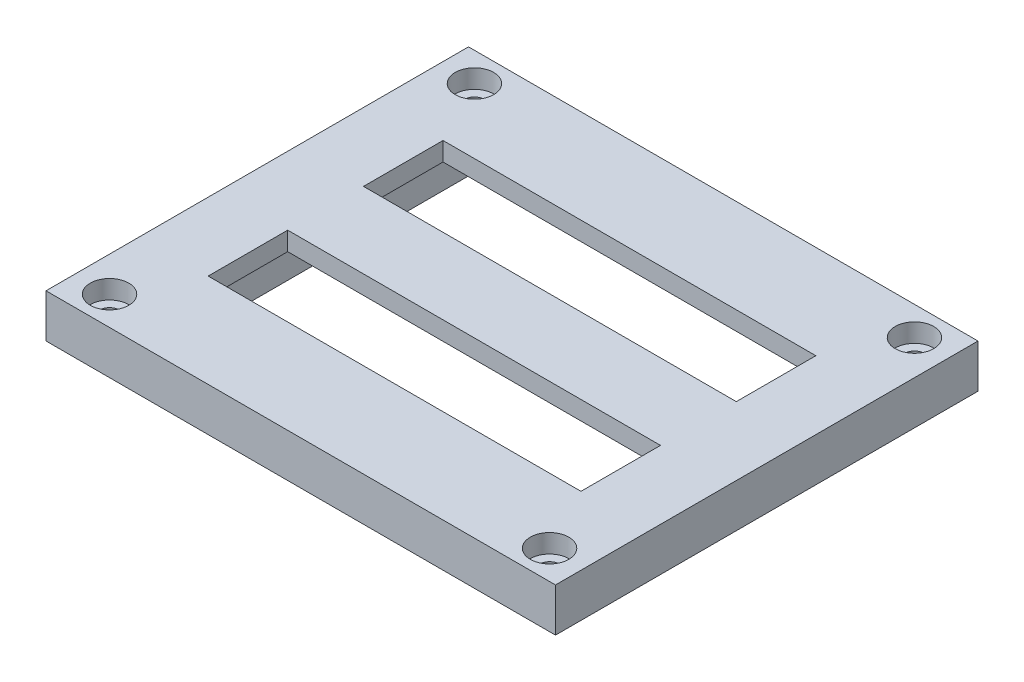
SolidWorks part; units mm, degrees
ref_plane "Спереди" through (0, 0, 0) normal (0, 0, 1) x (1, 0, 0)
ref_plane "Сверху" through (0, 0, 0) normal (0, 1, 0) x (1, 0, 0)
ref_plane "Справа" through (0, 0, 0) normal (1, 0, 0) x (0, 0, -1)
sketch "Sketch1" plane through (0, 0, 0) normal (0, 1, 0) x (1, 0, 0)
  line L1 (38, -31) -> (-38, -31)
  line L2 (38, -31) -> (38, 31)
  line L3 (38, 31) -> (-38, 31)
  line L4 (-38, -31) -> (-38, 31)
  line L5 (38, -31) -> (-38, 31) construction
  line L6 (38, 31) -> (-38, -31) construction
  point P0 (0, 0)
  dimension "D1" = 76
  dimension "D2" = 62
extrude "Boss-Extrude1" add sketch "Sketch1" along normal blind 2
sketch "Sketch2" plane through (0, 2, 0) normal (0, 1, 0) x (1, 0, 0)
  line L1 (-41, 34) -> (41, 34)
  line L2 (-41, 34) -> (-41, -34)
  line L3 (-41, -34) -> (41, -34)
  line L4 (41, 34) -> (41, -34)
  line L5 (-41, 34) -> (41, -34) construction
  line L6 (-41, -34) -> (41, 34) construction
  point P0 (0, 0)
  dimension "D1" = 82
  dimension "D2" = 68
extrude "Boss-Extrude2" add sketch "Sketch2" along normal blind 8
sketch "Sketch3" plane through (0, 0, 0) normal (0, -1, 0) x (1, 0, 0)
  line L0 (38, 0) -> (-38, 0) construction
  line L1 (0, -31) -> (0, 31) construction
  line L2 (38, -31) -> (-38, -31) construction
  line L3 (38, 31) -> (38, -31) construction
  line L4 (-38, -31) -> (-38, 31) construction
  line L5 (-38, 31) -> (38, 31) construction
  line L7 (-30, -18.9) -> (30, -18.9)
  line L8 (-30, -18.9) -> (-30, -6.1)
  line L9 (-30, 18.9) -> (30, 18.9)
  line L10 (-30, 18.9) -> (-30, 6.1)
  line L11 (-30, 6.1) -> (30, 6.1)
  line L12 (30, 18.9) -> (30, 6.1)
  line L13 (-30, 18.9) -> (30, 6.1) construction
  line L14 (-30, 6.1) -> (30, 18.9) construction
  line L15 (-30, -6.1) -> (30, -6.1)
  line L16 (30, -18.9) -> (30, -6.1)
  line L17 (-30, -18.9) -> (30, -6.1) construction
  line L18 (-30, -6.1) -> (30, -18.9) construction
  point P6 (0, 12.5)
  point P9 (0, -12.5)
  dimension "D1" = 60
  dimension "D2" = 12.8
  dimension "D3" = 25
  dimension "D4" = 12.5
extrude "Cut-Extrude1" cut sketch "Sketch3" against normal through all
sketch "Sketch4" plane through (0, 10, 0) normal (0, 1, 0) x (1, 0, 0)
  line L0 (41, 34) -> (-41, -34) construction
  line L1 (-41, 34) -> (41, -34) construction
  line L2 (-35.4089, 29.3635) -> (35.4089, 29.3635) construction
  line L3 (35.4089, 29.3635) -> (35.4089, -29.3635) construction
  line L4 (35.4089, -29.3635) -> (-35.4089, -29.3635) construction
  line L5 (-35.4089, -29.3635) -> (-35.4089, 29.3635) construction
  line L7 (-35.4089, -29.3635) -> (35.4089, 29.3635) construction
  line L8 (-35.4089, 29.3635) -> (35.4089, -29.3635) construction
  circle A0 centre (-35.4089, 29.3635) radius 1.6
  circle A1 centre (35.4089, 29.3635) radius 1.6
  circle A2 centre (35.4089, -29.3635) radius 1.6
  circle A3 centre (-35.4089, -29.3635) radius 1.6
  point P8 (0, 0)
  dimension "D2" = 3.2
  dimension "D1" = 92
extrude "Cut-Extrude2" cut sketch "Sketch4" against normal through all
sketch "Sketch5" plane through (0, 10, 0) normal (0, 1, 0) x (1, 0, 0)
  circle A0 centre (-35.4089, 29.3635) radius 3.1
  circle A1 centre (35.4089, 29.3635) radius 3.1
  circle A2 centre (35.4089, -29.3635) radius 3.1
  circle A3 centre (-35.4089, -29.3635) radius 3.1
  dimension "D1" = 6.2
extrude "Cut-Extrude3" cut sketch "Sketch5" against normal blind 3
sketch "Sketch9" plane through (0, 0, 0) normal (0, -1, 0) x (1, 0, 0)
  line L0 (-38, 31) -> (38, 31) construction
  line L1 (37.8, -30.8) -> (-37.8, -30.8)
  line L2 (37.8, -30.8) -> (37.8, 30.8)
  line L3 (37.8, 30.8) -> (-37.8, 30.8)
  line L4 (-37.8, -30.8) -> (-37.8, 30.8)
  line L5 (37.8, -30.8) -> (-37.8, 30.8) construction
  line L6 (37.8, 30.8) -> (-37.8, -30.8) construction
  line L7 (-38, -31) -> (-38, 31) construction
  point P0 (0, 0)
  dimension "D1" = 0.2
  dimension "D2" = 0.2
extrude "Cut-Extrude5" cut sketch "Sketch9" against normal blind 3 flip side to cut
sketch "Sketch10" plane through (0, 0, 0) normal (0, -1, 0) x (1, 0, 0)
  line L0 (-37.8, -30.8) -> (-31.8, -30.8)
  line L1 (-37.8, 24.8) -> (-37.8, 30.8)
  line L2 (34.7044, -30.8) -> (-34.7044, -30.8) construction
  line L3 (-37.8, 30.8) -> (-31.8, 30.8)
  line L4 (-31.8, -30.8) -> (-37.8, -24.8)
  line L5 (-37.8, 30.8) -> (-37.8, -30.8) construction
  line L6 (-37.8, -24.8) -> (-37.8, -30.8)
  line L7 (-34.7044, 30.8) -> (34.7044, 30.8) construction
  line L8 (-31.8, 30.8) -> (-37.8, 24.8)
  line L9 (37.8, 30.8) -> (37.8, 24.8)
  line L10 (37.8, -30.8) -> (37.8, 30.8) construction
  line L11 (37.8, 24.8) -> (31.8, 30.8)
  line L12 (31.8, 30.8) -> (37.8, 30.8)
  line L13 (37.8, -30.8) -> (31.8, -30.8)
  line L14 (31.8, -30.8) -> (37.8, -24.8)
  line L15 (37.8, -24.8) -> (37.8, -30.8)
  dimension "D1" = 6
extrude "Cut-Extrude6" cut sketch "Sketch10" against normal blind 3
sketch "Sketch11" plane through (0, 0, 0) normal (0, -1, 0) x (1, 0, 0)
  line L1 (-33, -27) -> (33, -27)
  line L2 (-33, -27) -> (-33, 27)
  line L3 (-33, 27) -> (33, 27)
  line L4 (33, -27) -> (33, 27)
  line L5 (-33, -27) -> (33, 27) construction
  line L6 (-33, 27) -> (33, -27) construction
  point P0 (0, 0)
  dimension "D1" = 54
  dimension "D2" = 66
extrude "Cut-Extrude7" cut sketch "Sketch11" against normal blind 7
chamfer "Chamfer2" distance 2 angle 10 2 edges at (-37.8, 0, 0) (37.8, 0, 0)
chamfer "Chamfer3" distance 1 angle 60 2 edges at (0, 0, 30.8) (0, 0, -30.8)
